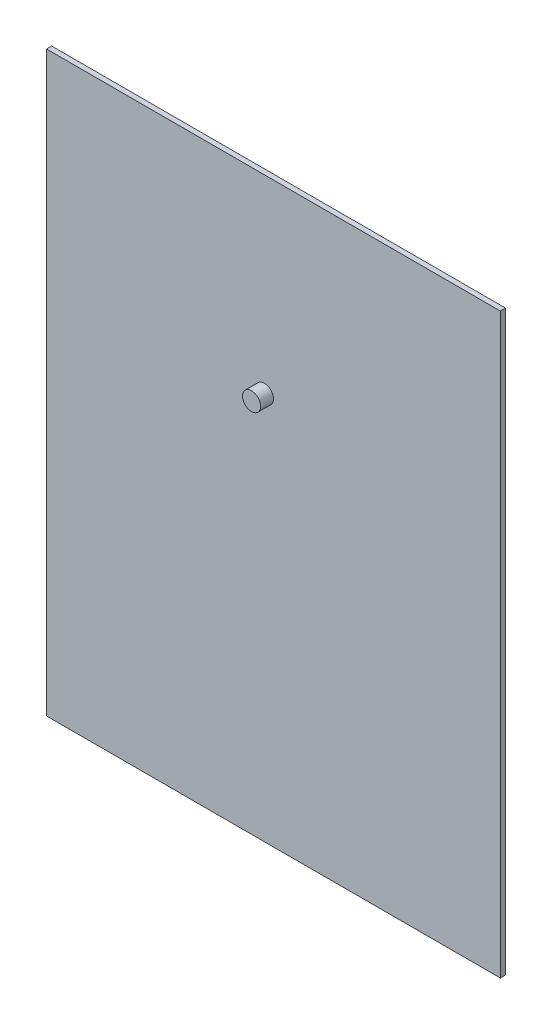
SolidWorks part; units mm, degrees
ref_plane "前视基准面" through (0, 0, 0) normal (0, 0, 1) x (1, 0, 0)
ref_plane "上视基准面" through (0, 0, 0) normal (0, 1, 0) x (1, 0, 0)
ref_plane "右视基准面" through (0, 0, 0) normal (1, 0, 0) x (0, 0, -1)
sketch "草图1" plane through (0, 0, 0) normal (0, 0, 1) x (1, 0, 0)
  line L0 (-45.8487, 35.4374) -> (130.1513, 35.4374)
  line L1 (130.1513, 35.4374) -> (130.1513, -188.5626)
  line L2 (130.1513, -188.5626) -> (-45.8487, -188.5626)
  line L3 (-45.8487, -188.5626) -> (-45.8487, 35.4374)
extrude "凸台-拉伸1" add sketch "草图1" along normal blind 2
sketch "草图2" plane through (0, 0, 2) normal (0, 0, 1) x (1, 0, 0)
  circle A0 centre (38.6653, -38.0719) radius 3.5
extrude "凸台-拉伸2" add sketch "草图2" along normal blind 5
